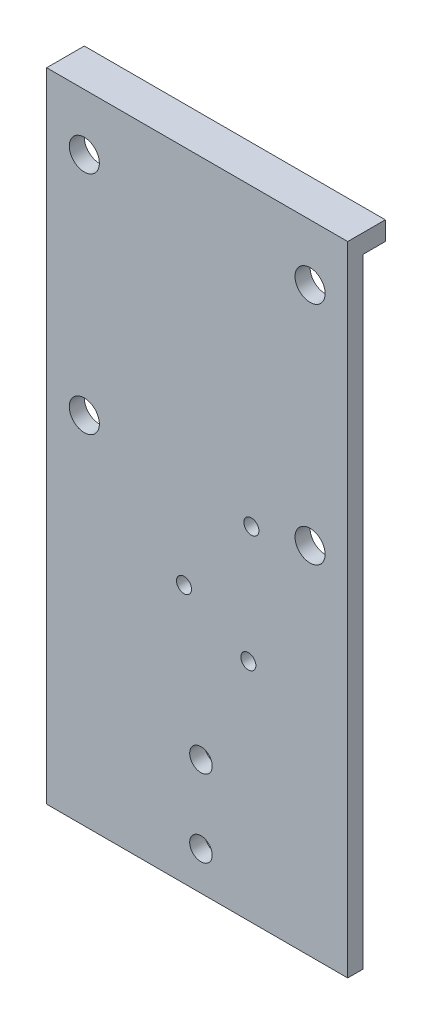
SolidWorks part; units mm, degrees
ref_plane "Plan de face" through (0, 0, 0) normal (0, 0, 1) x (1, 0, 0)
ref_plane "Plan de dessus" through (0, 0, 0) normal (0, 1, 0) x (1, 0, 0)
ref_plane "Plan de droite" through (0, 0, 0) normal (1, 0, 0) x (0, 0, -1)
sketch "Esquisse1" plane through (0, 0, 0) normal (0, 0, 1) x (1, 0, 0)
  line L1 (-29.009, 50.9055) -> (50.991, 50.9055)
  line L2 (-29.009, 50.9055) -> (-29.009, -118.5945)
  line L3 (-29.009, -118.5945) -> (50.991, -118.5945)
  line L4 (50.991, 50.9055) -> (50.991, -118.5945)
  dimension "D1" = 80
  dimension "D2" = 169.5
extrude "Boss.-Extru.1" add sketch "Esquisse1" along normal blind 4
sketch "Esquisse2" plane through (0, 0, 4) normal (0, 0, 1) x (1, 0, 0)
  line L0 (-19.009, 50.9055) -> (-19.009, -29.0945) construction
  line L1 (50.991, 50.9055) -> (-29.009, 50.9055) construction
  line L2 (40.991, 50.9055) -> (40.991, -29.0945) construction
  line L3 (-29.009, 35.9055) -> (50.991, 35.9055) construction
  line L4 (-29.009, 50.9055) -> (-29.009, -118.5945) construction
  line L5 (50.991, -118.5945) -> (50.991, 50.9055) construction
  line L6 (-29.009, -24.0945) -> (50.991, -24.0945) construction
  circle A0 centre (-19.009, 35.9055) radius 4
  circle A1 centre (40.991, 35.9055) radius 4
  circle A2 centre (-19.009, -24.0945) radius 4
  circle A3 centre (40.991, -24.0945) radius 4
  dimension "D6" = 8
  dimension "D7" = 8
  dimension "D8" = 8
  dimension "D9" = 8
  dimension "D1" = 80
  dimension "D2" = 15
  dimension "D3" = 60
  dimension "D4" = 10
  dimension "D5" = 10
extrude "Enlèv. mat.-Extru.1" cut sketch "Esquisse2" against normal through all
sketch "Esquisse5" plane through (0, 0, 4) normal (0, 0, 1) x (1, 0, 0)
  line L0 (10.991, -118.5945) -> (10.991, -35.3846) construction
  line L1 (-29.009, -118.5945) -> (50.991, -118.5945) construction
  line L2 (4.991, -118.5945) -> (4.991, -73.4707) construction
  line L3 (18.991, -73.4707) -> (18.991, -118.5945) construction
  line L4 (18.991, -118.5945) -> (18.991, -113.9278) construction
  line L5 (11.991, -73.4707) -> (11.991, -118.5945) construction
  circle A0 centre (11.991, -108.3445) radius 3
  circle A1 centre (11.991, -87.8445) radius 3
  dimension "D4" = 6
  dimension "D5" = 6
  dimension "D1" = 6
  dimension "D2" = 14
  dimension "D3" = 7
  dimension "D6" = 20.5
  dimension "D7" = 10.25
extrude "Enlèv. mat.-Extru.2" cut sketch "Esquisse5" against normal through all
sketch "Esquisse6" plane through (0, 0, 0) normal (0, 0, -1) x (-1, 0, 0)
  line L0 (29.009, 50.9055) -> (29.009, -118.5945) construction
  line L1 (-50.991, 50.9055) -> (29.009, 50.9055)
  line L2 (-50.991, 50.9055) -> (-50.991, 45.9055)
  line L3 (-50.991, 45.9055) -> (29.009, 45.9055)
  line L4 (29.009, 50.9055) -> (29.009, 45.9055)
  dimension "D1" = 5
extrude "Boss.-Extru.2" add sketch "Esquisse6" along normal blind 6
sketch "Esquisse7" plane through (0, 0, 4) normal (0, 0, 1) x (1, 0, 0)
  line L0 (-29.009, -118.5945) -> (50.991, -118.5945) construction
  line L5 (-29.009, 50.9055) -> (-29.009, -118.5945) construction
  line L6 (50.991, -118.5945) -> (50.991, 50.9055) construction
  line L7 (50.991, 50.9055) -> (-29.009, 50.9055) construction
  circle A0 centre (7.491, -49.8945) radius 2
  circle A1 centre (25.391, -27.4945) radius 2
  circle A2 centre (24.591, -58.8945) radius 2
  dimension "D5" = 4
  dimension "D6" = 4
  dimension "D7" = 4
  dimension "D9" = 68.7
  dimension "D10" = 26.4
  dimension "D11" = 59.7
  dimension "D12" = 78.4
  dimension "D13" = 25.6
  dimension "D8" = 36.5
extrude "Enlèv. mat.-Extru.5" cut sketch "Esquisse7" against normal through all
